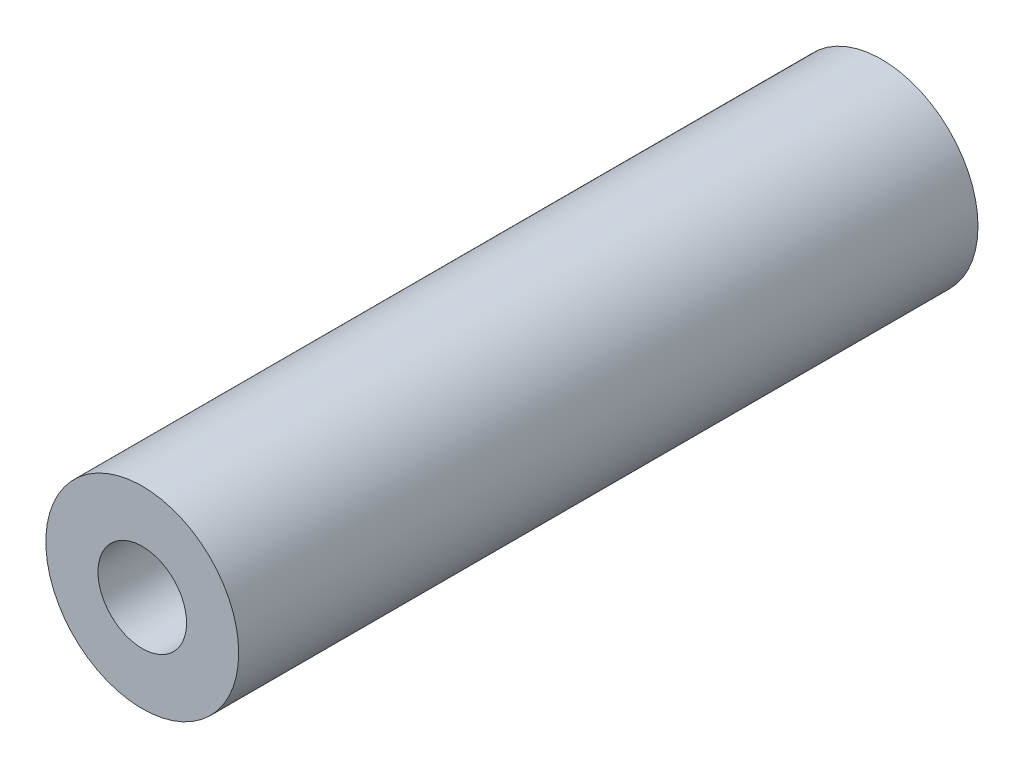
SolidWorks part; units mm, degrees
material "3003-O, Rod (SS)"
ref_plane "Front Plane" through (0, 0, 0) normal (0, 0, 1) x (1, 0, 0)
ref_plane "Top Plane" through (0, 0, 0) normal (0, 1, 0) x (1, 0, 0)
ref_plane "Right Plane" through (0, 0, 0) normal (1, 0, 0) x (0, 0, -1)
sketch "Sketch1" plane through (0, 0, 0) normal (0, 0, 1) x (1, 0, 0)
  circle A1 centre (0, 0) radius 38.1
  dimension "D2" = 76.2
extrude "Boss-Extrude1" add sketch "Sketch1" along normal blind 292.1
sketch "Sketch3" plane through (0, 0, 292.1) normal (0, 0, 1) x (1, 0, 0)
  line L0 (0, 38.1) -> (0, -38.1) construction
  line L1 (-38.1, 0) -> (38.1, 0) construction
  circle A0 centre (0, 0) radius 17.5
  circle A1 centre (0, 0) radius 38.1 construction
  dimension "D1" = 35
extrude "Cut-Extrude1" cut sketch "Sketch3" against normal through all both and the other way through all
